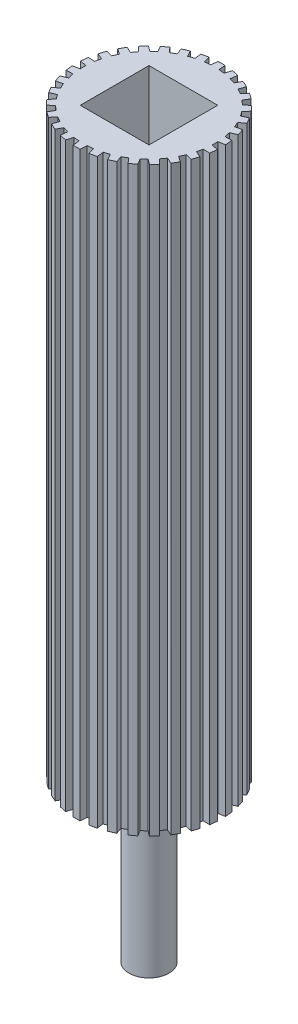
SolidWorks part; units mm, degrees
ref_plane "Front Plane" through (0, 0, 0) normal (0, 0, 1) x (1, 0, 0)
ref_plane "Top Plane" through (0, 0, 0) normal (0, 1, 0) x (1, 0, 0)
ref_plane "Right Plane" through (0, 0, 0) normal (1, 0, 0) x (0, 0, -1)
sketch "Sketch2" plane through (0, 0, 0) normal (0, 1, 0) x (1, 0, 0)
  line L1 (-0.7753, 12.6763) -> (-0.6703, 13.9539)
  line L2 (0.7753, 12.6763) -> (0.6703, 13.9539)
  line L3 (1.8772, 12.5605) -> (2.2456, 13.7883)
  line L4 (3.3939, 12.2381) -> (3.5568, 13.5096)
  line L5 (4.4476, 11.8957) -> (5.0633, 13.0201)
  line L6 (5.8642, 11.265) -> (6.2879, 12.4749)
  line L7 (6.8237, 10.7111) -> (7.6597, 11.6829)
  line L8 (8.0782, 9.7996) -> (8.7442, 10.895)
  line L9 (8.9015, 9.0583) -> (9.9213, 9.8351)
  line L10 (9.9391, 7.9059) -> (10.8183, 8.8389)
  line L11 (10.5903, 7.0096) -> (11.7493, 7.5574)
  line L12 (11.3657, 5.6667) -> (12.4196, 6.3965)
  line L13 (11.8163, 4.6546) -> (13.0638, 4.9494)
  line L14 (12.2955, 3.1798) -> (13.4781, 3.6745)
  line L15 (12.5258, 2.0961) -> (13.8074, 2.1252)
  line L16 (12.6879, 0.554) -> (13.9475, 0.792)
  line L17 (12.6879, -0.554) -> (13.9475, -0.792)
  line L18 (12.5258, -2.0961) -> (13.8074, -2.1252)
  line L19 (12.2955, -3.1798) -> (13.4781, -3.6745)
  line L20 (11.8163, -4.6546) -> (13.0638, -4.9494)
  line L21 (11.3657, -5.6667) -> (12.4196, -6.3965)
  line L22 (10.5903, -7.0096) -> (11.7493, -7.5574)
  line L23 (9.9391, -7.9059) -> (10.8183, -8.8389)
  line L24 (8.9015, -9.0583) -> (9.9213, -9.8351)
  line L25 (8.0782, -9.7996) -> (8.7442, -10.895)
  line L26 (6.8237, -10.7111) -> (7.6597, -11.6829)
  line L27 (5.8642, -11.265) -> (6.2879, -12.4749)
  line L28 (4.4476, -11.8957) -> (5.0633, -13.0201)
  line L29 (3.3939, -12.2381) -> (3.5568, -13.5096)
  line L30 (1.8772, -12.5605) -> (2.2456, -13.7883)
  line L31 (0.7753, -12.6763) -> (0.6703, -13.9539)
  line L32 (-0.7753, -12.6763) -> (-0.6703, -13.9539)
  line L33 (-1.8772, -12.5605) -> (-2.2456, -13.7883)
  line L34 (-3.3939, -12.2381) -> (-3.5568, -13.5096)
  line L35 (-4.4476, -11.8957) -> (-5.0633, -13.0201)
  line L36 (-5.8642, -11.265) -> (-6.2879, -12.4749)
  line L37 (-6.8237, -10.7111) -> (-7.6597, -11.6829)
  line L38 (-8.0782, -9.7996) -> (-8.7442, -10.895)
  line L39 (-8.9015, -9.0583) -> (-9.9213, -9.8351)
  line L40 (-9.9391, -7.9059) -> (-10.8183, -8.8389)
  line L41 (-10.5903, -7.0096) -> (-11.7493, -7.5574)
  line L42 (-11.3657, -5.6667) -> (-12.4196, -6.3965)
  line L43 (-11.8163, -4.6546) -> (-13.0638, -4.9494)
  line L44 (-12.2955, -3.1798) -> (-13.4781, -3.6745)
  line L45 (-12.5258, -2.0961) -> (-13.8074, -2.1252)
  line L46 (-12.6879, -0.554) -> (-13.9475, -0.792)
  line L47 (-12.6879, 0.554) -> (-13.9475, 0.792)
  line L48 (-12.5258, 2.0961) -> (-13.8074, 2.1252)
  line L49 (-12.2955, 3.1798) -> (-13.4781, 3.6745)
  line L50 (-11.8163, 4.6546) -> (-13.0638, 4.9494)
  line L51 (-11.3657, 5.6667) -> (-12.4196, 6.3965)
  line L52 (-10.5903, 7.0096) -> (-11.7493, 7.5574)
  line L53 (-9.9391, 7.9059) -> (-10.8183, 8.8389)
  line L54 (-8.9015, 9.0583) -> (-9.9213, 9.8351)
  line L55 (-8.0782, 9.7996) -> (-8.7442, 10.895)
  line L56 (-6.8237, 10.7111) -> (-7.6597, 11.6829)
  line L57 (-5.8642, 11.265) -> (-6.2879, 12.4749)
  line L58 (-4.4476, 11.8957) -> (-5.0633, 13.0201)
  line L59 (-3.3939, 12.2381) -> (-3.5568, 13.5096)
  line L60 (-1.8772, 12.5605) -> (-2.2456, 13.7883)
  arc A0 (-2.2456, 13.7883) -> (-3.5568, 13.5096) centre (0, 0) ccw
  arc A1 (-0.7753, 12.6763) -> (-1.8772, 12.5605) centre (0, 0) ccw
  arc A3 (-3.3939, 12.2381) -> (-4.4476, 11.8957) centre (0, 0) ccw
  arc A4 (-5.0633, 13.0201) -> (-6.2879, 12.4749) centre (0, 0) ccw
  arc A5 (-5.8642, 11.265) -> (-6.8237, 10.7111) centre (0, 0) ccw
  arc A6 (-7.6597, 11.6829) -> (-8.7442, 10.895) centre (0, 0) ccw
  arc A7 (-8.0782, 9.7996) -> (-8.9015, 9.0583) centre (0, 0) ccw
  arc A8 (-9.9213, 9.8351) -> (-10.8183, 8.8389) centre (0, 0) ccw
  arc A9 (-9.9391, 7.9059) -> (-10.5903, 7.0096) centre (0, 0) ccw
  arc A10 (-11.7493, 7.5574) -> (-12.4196, 6.3965) centre (0, 0) ccw
  arc A11 (-11.3657, 5.6667) -> (-11.8163, 4.6546) centre (0, 0) ccw
  arc A12 (-13.0638, 4.9494) -> (-13.4781, 3.6745) centre (0, 0) ccw
  arc A13 (-12.2955, 3.1798) -> (-12.5258, 2.0961) centre (0, 0) ccw
  arc A14 (-13.8074, 2.1252) -> (-13.9475, 0.792) centre (0, 0) ccw
  arc A15 (-12.6879, 0.554) -> (-12.6879, -0.554) centre (0, 0) ccw
  arc A16 (-13.9475, -0.792) -> (-13.8074, -2.1252) centre (0, 0) ccw
  arc A17 (-12.5258, -2.0961) -> (-12.2955, -3.1798) centre (0, 0) ccw
  arc A18 (-13.4781, -3.6745) -> (-13.0638, -4.9494) centre (0, 0) ccw
  arc A19 (-11.8163, -4.6546) -> (-11.3657, -5.6667) centre (0, 0) ccw
  arc A20 (-12.4196, -6.3965) -> (-11.7493, -7.5574) centre (0, 0) ccw
  arc A21 (-10.5903, -7.0096) -> (-9.9391, -7.9059) centre (0, 0) ccw
  arc A22 (-10.8183, -8.8389) -> (-9.9213, -9.8351) centre (0, 0) ccw
  arc A23 (-8.9015, -9.0583) -> (-8.0782, -9.7996) centre (0, 0) ccw
  arc A24 (-8.7442, -10.895) -> (-7.6597, -11.6829) centre (0, 0) ccw
  arc A25 (-6.8237, -10.7111) -> (-5.8642, -11.265) centre (0, 0) ccw
  arc A26 (-6.2879, -12.4749) -> (-5.0633, -13.0201) centre (0, 0) ccw
  arc A27 (-4.4476, -11.8957) -> (-3.3939, -12.2381) centre (0, 0) ccw
  arc A28 (-3.5568, -13.5096) -> (-2.2456, -13.7883) centre (0, 0) ccw
  arc A29 (-1.8772, -12.5605) -> (-0.7753, -12.6763) centre (0, 0) ccw
  arc A30 (-0.6703, -13.9539) -> (0.6703, -13.9539) centre (0, 0) ccw
  arc A31 (0.7753, -12.6763) -> (1.8772, -12.5605) centre (0, 0) ccw
  arc A32 (2.2456, -13.7883) -> (3.5568, -13.5096) centre (0, 0) ccw
  arc A33 (3.3939, -12.2381) -> (4.4476, -11.8957) centre (0, 0) ccw
  arc A34 (5.0633, -13.0201) -> (6.2879, -12.4749) centre (0, 0) ccw
  arc A35 (5.8642, -11.265) -> (6.8237, -10.7111) centre (0, 0) ccw
  arc A36 (7.6597, -11.6829) -> (8.7442, -10.895) centre (0, 0) ccw
  arc A37 (8.0782, -9.7996) -> (8.9015, -9.0583) centre (0, 0) ccw
  arc A38 (9.9213, -9.8351) -> (10.8183, -8.8389) centre (0, 0) ccw
  arc A39 (9.9391, -7.9059) -> (10.5903, -7.0096) centre (0, 0) ccw
  arc A40 (11.7493, -7.5574) -> (12.4196, -6.3965) centre (0, 0) ccw
  arc A41 (11.3657, -5.6667) -> (11.8163, -4.6546) centre (0, 0) ccw
  arc A42 (13.0638, -4.9494) -> (13.4781, -3.6745) centre (0, 0) ccw
  arc A43 (12.2955, -3.1798) -> (12.5258, -2.0961) centre (0, 0) ccw
  arc A44 (13.8074, -2.1252) -> (13.9475, -0.792) centre (0, 0) ccw
  arc A45 (12.6879, -0.554) -> (12.6879, 0.554) centre (0, 0) ccw
  arc A46 (13.9475, 0.792) -> (13.8074, 2.1252) centre (0, 0) ccw
  arc A47 (12.5258, 2.0961) -> (12.2955, 3.1798) centre (0, 0) ccw
  arc A48 (13.4781, 3.6745) -> (13.0638, 4.9494) centre (0, 0) ccw
  arc A49 (0.6703, 13.9539) -> (-0.6703, 13.9539) centre (0, 0) ccw
  arc A50 (3.5568, 13.5096) -> (2.2456, 13.7883) centre (0, 0) ccw
  arc A51 (6.2879, 12.4749) -> (5.0633, 13.0201) centre (0, 0) ccw
  arc A52 (8.7442, 10.895) -> (7.6597, 11.6829) centre (0, 0) ccw
  arc A53 (1.8772, 12.5605) -> (0.7753, 12.6763) centre (0, 0) ccw
  arc A54 (4.4476, 11.8957) -> (3.3939, 12.2381) centre (0, 0) ccw
  arc A55 (6.8237, 10.7111) -> (5.8642, 11.265) centre (0, 0) ccw
  arc A56 (8.9015, 9.0583) -> (8.0782, 9.7996) centre (0, 0) ccw
  arc A57 (10.5903, 7.0096) -> (9.9391, 7.9059) centre (0, 0) ccw
  arc A58 (10.8183, 8.8389) -> (9.9213, 9.8351) centre (0, 0) ccw
  arc A59 (12.4196, 6.3965) -> (11.7493, 7.5574) centre (0, 0) ccw
  arc A60 (11.8163, 4.6546) -> (11.3657, 5.6667) centre (0, 0) ccw
  point P129 (0, 0)
  dimension "D1" = 30
extrude "Boss-Extrude1" add sketch "Sketch2" along normal blind 211.1375 contours L39 A22 L40 A21 L41 A20 L42 A19 L43 A18 L44 A17 L45 A16 L46 A15 L47 A14 L48 A13 L49 A12 L50 A11 L51 A10 L52 A9 L53 A8 L54 A7 L55 A6 L56 A5 L57 A4 L58 A3 L59 A0 L60 A1 L1 A49 L2 A53 L3 A50 L4 A54 L5 A51 L6 A55 L7 A52 L8 A56 L9 A58 L10 A57 L11 A59 L12 A60 L13 A48 L14 A47 L15 A46 L16 A45 L17 A44 L18 A43 L19 A42 L20 A41 L21 A40 L22 A39 L23 A38 L24 A37 L25 A36 L26 A35 L27 A34 L28 A33 L29 A32 L30 A31 L31 A30 L32 A29 L33 A28 L34 A27 L35 A26 L36 A25 L37 A24 L38 A23
scale "Scale2" scale about centroid uniform scaling no x scale factor 0.96 y scale factor 1 z scale factor 0.96
sketch "Sketch3" plane through (0, 211.1375, 0) normal (0, 1, 0) x (1, 0, 0)
  circle A0 centre (0, 0) radius 3.6805
  dimension "D1" = 7.3609
extrude "Boss-Extrude2" add sketch "Sketch3" along normal blind 23.2093
sketch "Sketch4" plane through (0, 0, 0) normal (0, -1, 0) x (-1, 0, 0)
  circle A0 centre (0, 0) radius 3.6805
  dimension "D1" = 7.3609
extrude "Boss-Extrude3" add sketch "Sketch4" along normal blind 29.5593
sketch "Sketch6" plane through (0, 234.3467, 0) normal (0, 1, 0) x (1, 0, 0)
  line L1 (-2.286, -2.286) -> (2.286, -2.286)
  line L2 (-2.286, -2.286) -> (-2.286, 2.286)
  line L3 (-2.286, 2.286) -> (2.286, 2.286)
  line L4 (2.286, -2.286) -> (2.286, 2.286)
  line L9 (-2.286, -2.286) -> (2.286, 2.286) construction
  line L10 (-2.286, 2.286) -> (2.286, -2.286) construction
  point P0 (0, 0)
  dimension "D1" = 4.572
  dimension "D2" = 4.572
extrude "Boss-Extrude4" add sketch "Sketch6" along normal blind 10.16
sketch "Sketch7" plane through (0, 244.5067, 0) normal (0, 1, 0) x (1, 0, 0)
  circle A0 centre (0, 0) radius 18.9421
extrude "Cut-Extrude1" cut sketch "Sketch7" against normal blind 137.033
sketch "Sketch8" plane through (0, 107.4738, 0) normal (0, 1, 0) x (1, 0, 0)
  line L1 (-6.35, -6.35) -> (6.35, -6.35)
  line L2 (-6.35, -6.35) -> (-6.35, 6.35)
  line L3 (-6.35, 6.35) -> (6.35, 6.35)
  line L4 (6.35, -6.35) -> (6.35, 6.35)
  line L5 (-6.35, -6.35) -> (6.35, 6.35) construction
  line L6 (-6.35, 6.35) -> (6.35, -6.35) construction
  point P0 (0, 0)
  dimension "D1" = 12.7
  dimension "D2" = 12.7
extrude "Cut-Extrude2" cut sketch "Sketch8" against normal blind 12.7
